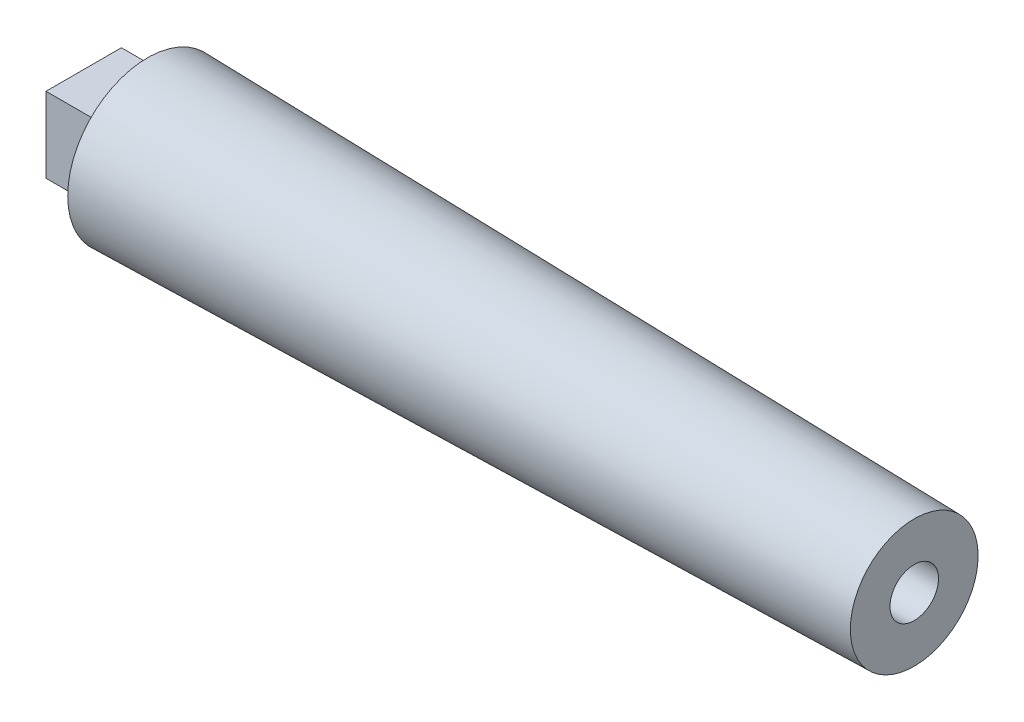
SolidWorks part; units mm, degrees
ref_plane "Front Plane" through (0, 0, 0) normal (0, 0, 1) x (1, 0, 0)
ref_plane "Top Plane" through (0, 0, 0) normal (0, 1, 0) x (1, 0, 0)
ref_plane "Right Plane" through (0, 0, 0) normal (1, 0, 0) x (0, 0, -1)
sketch "Sketch1" plane through (0, 0, 0) normal (0, 0, 1) x (1, 0, 0)
  line L0 (0, 0) -> (233.3556, 0) construction
  line L1 (0, 0) -> (152.4, 0)
  line L2 (152.4, 0) -> (152.4, 12.7)
  line L3 (152.4, 12.7) -> (0, 15.875)
  line L4 (0, 15.875) -> (0, 0)
  dimension "D1" = 152.4
  dimension "D2" = 12.7
  dimension "D3" = 15.875
revolve "Revolve1" add sketch "Sketch1" angle 360 about L0
sketch "Sketch2" plane through (152.4, 0, 0) normal (1, 0, 0) x (0, 0, -1)
  circle A0 centre (0, 0) radius 4.826
extrude "Cut-Extrude1" cut sketch "Sketch2" against normal blind 25.4
sketch "Sketch3" plane through (0, 0, 0) normal (-1, 0, 0) x (0, 0, 1)
  line L1 (-7.493, -7.493) -> (7.493, -7.493)
  line L2 (-7.493, -7.493) -> (-7.493, 7.493)
  line L3 (-7.493, 7.493) -> (7.493, 7.493)
  line L4 (7.493, -7.493) -> (7.493, 7.493)
  line L5 (-7.493, -7.493) -> (7.493, 7.493) construction
  line L6 (-7.493, 7.493) -> (7.493, -7.493) construction
  point P0 (0, 0)
  dimension "D1" = 14.986
  dimension "D2" = 14.986
extrude "Boss-Extrude1" add sketch "Sketch3" along normal blind 12.7
